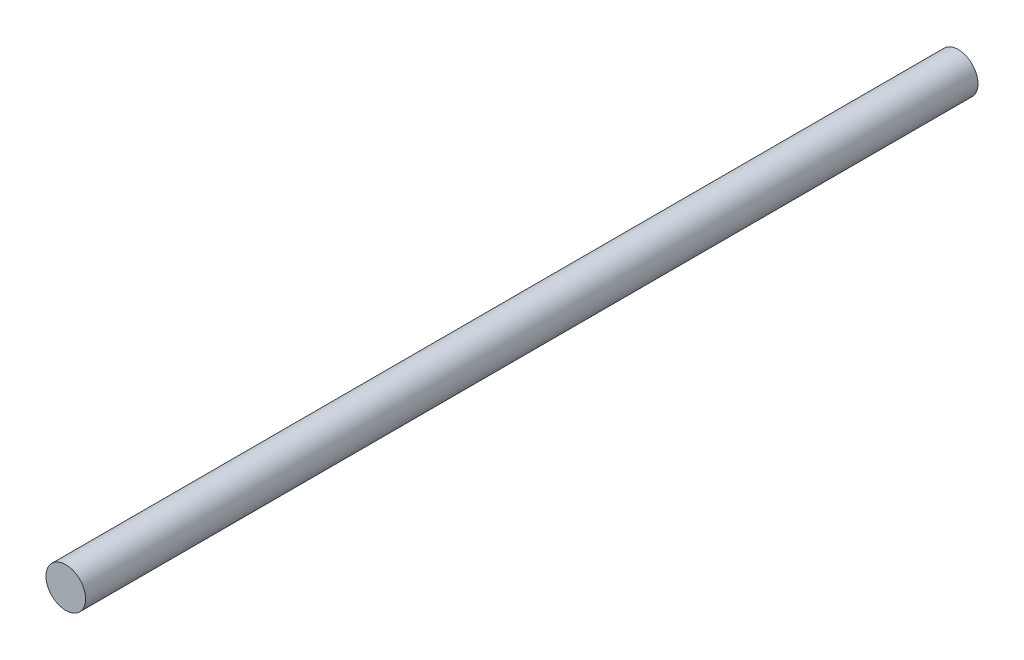
SolidWorks part; units mm, degrees
ref_plane "Front Plane" through (0, 0, 0) normal (0, 0, 1) x (1, 0, 0)
ref_plane "Top Plane" through (0, 0, 0) normal (0, 1, 0) x (1, 0, 0)
ref_plane "Right Plane" through (0, 0, 0) normal (1, 0, 0) x (0, 0, -1)
sketch "Sketch1" plane through (0, 0, 0) normal (0, 0, 1) x (1, 0, 0)
  circle A0 centre (0, 0) radius 3.175
extrude "Boss-Extrude1" add sketch "Sketch1" along normal blind 142.875
